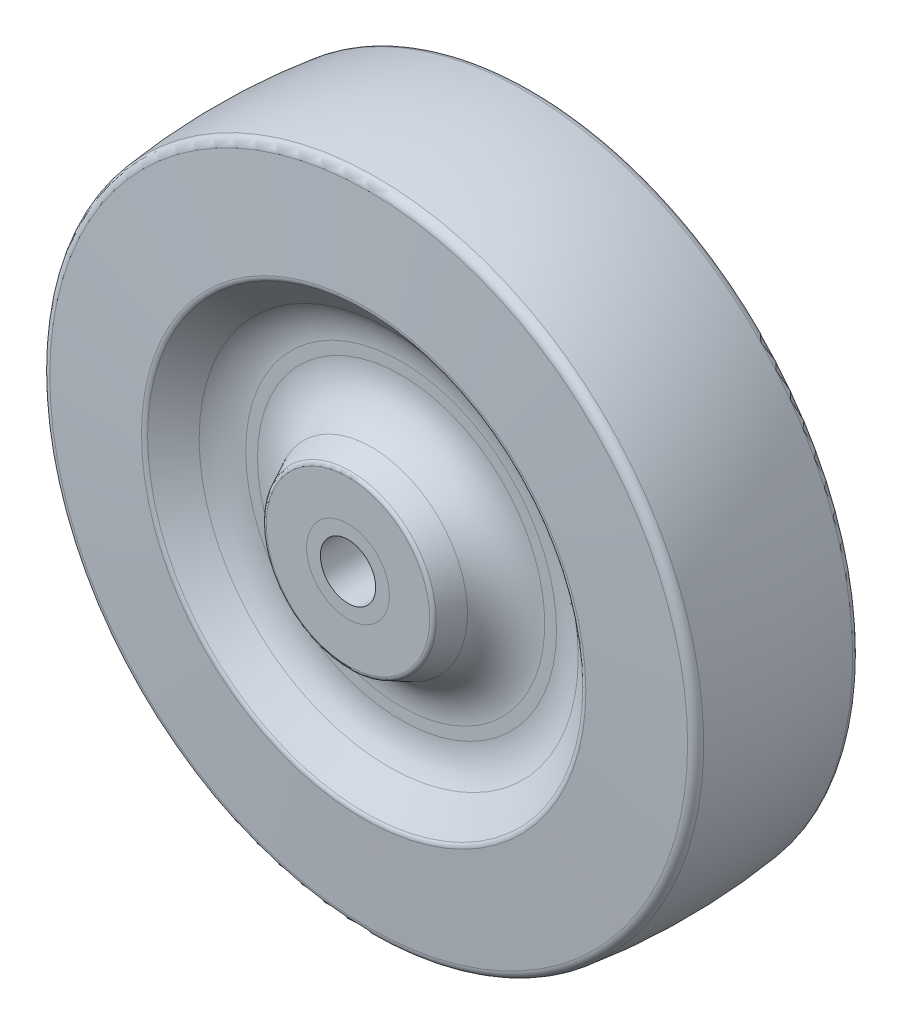
SolidWorks part; units mm, degrees
ref_plane "Front Plane" through (0, 0, 0) normal (0, 0, 1) x (1, 0, 0)
ref_plane "Top Plane" through (0, 0, 0) normal (0, 1, 0) x (1, 0, 0)
ref_plane "Right Plane" through (0, 0, 0) normal (1, 0, 0) x (0, 0, -1)
sketch "Sketch1" plane through (0, 0, 0) normal (1, 0, 0) x (0, 0, -1)
  line L0 (0, -38.1) -> (0, 38.1) construction
  line L1 (-11.8237, 0) -> (11.8237, 0) construction
  line L2 (-10.0457, 38.1) -> (10.0457, 38.1) construction
  point P0 (0, 3.175)
  point P3 (0, -3.175)
  point P4 (0, 0)
  point P8 (0, 0)
  point P11 (0, 38.1)
  point P14 (0, 4.7498)
  point P16 (0, -4.7498)
  point P17 (11.8237, 0)
  dimension "Wheel Diameter" = 76.2
  dimension "Hub Length" = 23.6474
  dimension "Wheel Width" = 20.0914
  dimension "For Axle Diameter" = 6.35
  dimension "D2" = 3.175
  dimension "Sleeve Bearing Diameter" = 9.4996
sketch "Sketch2" plane through (0, 0, 0) normal (1, 0, 0) x (0, 0, -1)
  line L6 (10.0457, 38.1) -> (0, 38.1) construction
  line L8 (0, 0) -> (0, 38.1) construction
  line L9 (0, -38.1) -> (0, 38.1) construction
  line L13 (5.7277, 20.066) -> (10.0457, 20.066) construction
  line L25 (5.7277, 12.7) -> (10.0457, 12.7) construction
  line L26 (-10.0457, 38.1) -> (0, 38.1) construction
  line L27 (10.0457, 25.212) -> (10.0457, 37.3738) construction
  line L28 (10.0457, 25.212) -> (5.7277, 20.066)
  line L29 (5.7277, 20.066) -> (5.7277, 12.7)
  line L30 (-11.8237, 0) -> (11.8237, 0) construction
  line L31 (11.8237, 9.7028) -> (5.7277, 12.7)
  line L33 (11.8237, 9.7028) -> (11.8237, 0)
  line L38 (-11.8237, 0) -> (11.8237, 0)
  line L39 (10.0457, 25.212) -> (9.4036, 37.4641)
  line L40 (-11.8237, 9.7028) -> (-11.8237, 0)
  line L41 (-11.8237, 9.7028) -> (-5.7277, 12.7)
  line L42 (-5.7277, 20.066) -> (-5.7277, 12.7)
  line L43 (-10.0457, 25.212) -> (-5.7277, 20.066)
  line L44 (-10.0457, 25.212) -> (-9.4036, 37.4641)
  arc A0 (0, 38.1) -> (10.0457, 37.3738) centre (0, -31.75) cw construction
  arc A1 (-9.4036, 37.4641) -> (9.4036, 37.4641) centre (0, -31.75) cw
  point P25 (0, 0)
  dimension "D3" = 12.7
  dimension "D4" = 9.7028
  dimension "D5" = 20.066
  dimension "D6" = 69.85
  dimension "D7" = 3
  dimension "D1" = 50
  dimension "D2" = 4.318
revolve "Revolve1" add sketch "Sketch2" angle 360 about L38
sketch "Sketch3" plane through (0, 0, 0) normal (1, 0, 0) x (0, 0, -1)
  line L12 (-11.8237, 0) -> (11.8237, 0) construction
  line L20 (11.8237, 0) -> (11.8237, 4.7498)
  line L21 (11.8237, 4.7498) -> (-11.8237, 4.7498)
  line L22 (-11.8237, 0) -> (-11.8237, 4.7498)
  line L25 (-11.8237, 0) -> (11.8237, 0)
  point P0 (0, 0)
revolve "Revolve2" add sketch "Sketch3" angle 360 about L25
sketch "Sketch6" plane through (0, 0, 0) normal (1, 0, 0) x (0, 0, -1)
  line L0 (0, -38.1) -> (0, 38.1) construction
  line L1 (-11.8237, 4.7498) -> (11.8237, 4.7498)
  line L5 (11.8237, 0) -> (-11.8237, 0)
  line L8 (-11.8237, 4.7498) -> (-11.8237, 0)
  line L9 (11.8237, 4.7498) -> (11.8237, 0)
  point P6 (0, 4.7498)
  point P11 (0, 0)
revolve "Cut-Revolve1" cut sketch "Sketch6" angle 360 about L1
sketch "Sketch4" plane through (0, 0, 0) normal (0, 0, 1) x (1, 0, 0)
  line L0 (0, -38.1) -> (0, 38.1) construction
  circle A0 centre (0, 0) radius 3.175
extrude "Cut-Extrude1" cut sketch "Sketch4" against normal through all both and the other way through all
fillet "Fillet1" radius 1.016 2 edges at (37.4641, 0, 9.4036) (37.4641, 0, -9.4036)
fillet "Fillet2" radius 6.096 4 edges at (20.066, 0, -5.7277) (12.7, 0, -5.7277) (12.7, 0, 5.7277) (20.066, 0, 5.7277)
fillet "Fillet3" radius 0.762 2 edges at (25.212, 0, 10.0457) (25.212, 0, -10.0457)
fillet "Fillet4" radius 0.508 2 edges at (9.7028, 0, -11.8237) (9.7028, 0, 11.8237)
sketch "Sketch8" plane through (0, 0, 0) normal (1, 0, 0) x (0, 0, -1)
  line L0 (0, -38.1) -> (0, 38.1) construction
  line L2 (-10.0457, 38.1) -> (10.0457, 38.1) construction
  line L3 (-11.8237, 0) -> (11.8237, 0) construction
  point P0 (10.0457, 33.02)
  point P5 (0, 0)
  point P6 (-10.0457, 33.02)
  point P12 (11.8237, -8.89)
  point P13 (-11.8237, -8.89)
  dimension "D1" = 5.08
  dimension "D2" = 8.89
sketch "Sketch9" plane through (0, 0, 0) normal (0, 0, 1) x (1, 0, 0)
  circle A0 centre (0, 0) radius 38.1 construction
  circle A1 centre (0, 0) radius 3.175 construction
equation "\"D2@Sketch1\" = \"For Axle Diameter@Sketch1\" / 2"
